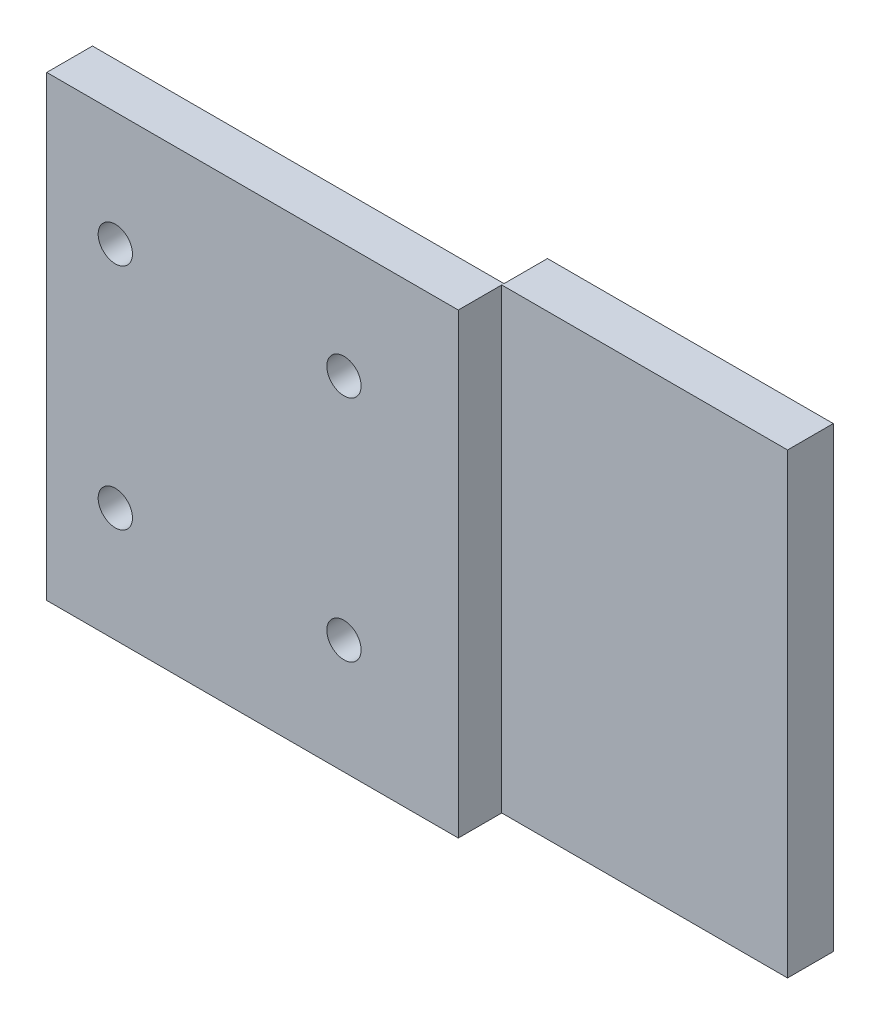
SolidWorks part; units mm, degrees
ref_plane "Спереди" through (0, 0, 0) normal (0, 0, 1) x (1, 0, 0)
ref_plane "Сверху" through (0, 0, 0) normal (0, 1, 0) x (1, 0, 0)
ref_plane "Справа" through (0, 0, 0) normal (1, 0, 0) x (0, 0, -1)
sketch "Эскиз1" plane through (0, 0, 0) normal (0, 0, 1) x (1, 0, 0)
  line L0 (0, 0) -> (36, 0)
  line L1 (0, 0) -> (0, 40)
  line L2 (36, 0) -> (36, 40)
  line L3 (0, 40) -> (36, 40)
  line L4 (6, 30) -> (26, 30) construction
  line L5 (26, 30) -> (26, 10) construction
  line L6 (26, 10) -> (6, 10) construction
  line L7 (6, 10) -> (6, 30) construction
  line L8 (18, 40) -> (18, 0) construction
  circle A0 centre (6, 30) radius 1.5
  circle A1 centre (26, 30) radius 1.5
  circle A2 centre (26, 10) radius 1.5
  circle A3 centre (6, 10) radius 1.5
  dimension "D1" = 3
  dimension "D2" = 3
  dimension "D3" = 3
  dimension "D4" = 3
  dimension "D5" = 20
  dimension "D6" = 20
  dimension "D7" = 40
  dimension "D8" = 36
  dimension "D9" = 10
  dimension "D10" = 10
  dimension "D11" = 6
extrude "Бобышка-Вытянуть1" add sketch "Эскиз1" along normal blind 4
sketch "Эскиз2" plane through (36, 0, 0) normal (1, 0, 0) x (0, 0, -1)
  line L0 (-14.3, -172.2152) -> (-14.3, 207.7848) construction
  line L1 (-14.3, -172.2152) -> (-14.3, 207.7848) construction
  line L2 (-16.3, 207.7848) -> (-16.3, -172.2152) construction
  line L3 (-16.3, 207.7848) -> (-16.3, -172.2152) construction
  line L4 (-0.2, -172.2152) -> (-0.2, 207.7848) construction
  line L5 (-0.2, -172.2152) -> (-0.2, 207.7848) construction
  line L6 (-2.2, 207.7848) -> (-2.2, -172.2152) construction
  line L7 (-2.2, 207.7848) -> (-2.2, -172.2152) construction
sketch "Эскиз11" plane through (0, 0, 0) normal (0, -1, 0) x (1, 0, 0)
  line L0 (47.25, 14.3) -> (47.25, 2.2) construction
  line L1 (39.85, 2.2) -> (39.85, 14.3) construction
  line L2 (47.25, 14.3) -> (47.25, 2.2)
  line L3 (39.85, 2.2) -> (39.85, 14.3)
sketch "Эскиз12" plane through (0, 0, 0) normal (-1, 0, 0) x (0, 0, 1)
  line L0 (16.3, -104.158) -> (16.3, 108.842) construction
  line L1 (14.3, -104.158) -> (14.3, 108.842) construction
  line L2 (16.3, -104.158) -> (16.3, 108.842)
  line L3 (14.3, -104.158) -> (14.3, 108.842)
  line L4 (2.2, 108.842) -> (2.2, -104.158) construction
  line L5 (0.2, 108.842) -> (0.2, -104.158) construction
  line L6 (2.2, 108.842) -> (2.2, -104.158)
  line L7 (0.2, 108.842) -> (0.2, -104.158)
sketch "Эскиз13" plane through (36, 0, 0) normal (1, 0, 0) x (0, 0, -1)
  line L0 (-0.2, 0) -> (-0.2, 40)
  line L1 (-0.2, 0) -> (3.8, 0)
  line L2 (-0.2, 40) -> (3.8, 40)
  line L3 (3.8, 0) -> (3.8, 40)
  line L4 (-4, 0) -> (0, 0) construction
  line L5 (-4, 40) -> (0, 40) construction
  line L7 (0, 0) -> (0, 40) construction
  dimension "D1" = 0.2
  dimension "D2" = 4
extrude "Бобышка-Вытянуть2" add sketch "Эскиз13" along normal blind 25
sketch "Эскиз14" plane through (0, 0, 0.2) normal (0, 0, 1) x (1, 0, 0)
  line L0 (47.25, 0) -> (47.25, 40) construction
  line L1 (61, 0) -> (36, 0) construction
  line L2 (61, 40) -> (36, 40) construction
  line L3 (39.85, 0) -> (39.85, 40) construction
  line L4 (61, 40) -> (61, 0) construction
  line L5 (27.55, 37) -> (59.55, 37)
  line L6 (27.55, 37) -> (27.55, 3)
  line L7 (59.55, 37) -> (59.55, 3)
  line L8 (27.55, 3) -> (59.55, 3)
  line L9 (39.85, 40) -> (47.25, 40) construction
  line L10 (43.55, 40) -> (43.55, 0) construction
  line L11 (43.55, 37) -> (43.55, 3) construction
  dimension "D1" = 13.75
  dimension "D2" = 7.4
  dimension "D3" = 34
  dimension "D4" = 32
  dimension "D5" = 3
  dimension "D6" = 3
